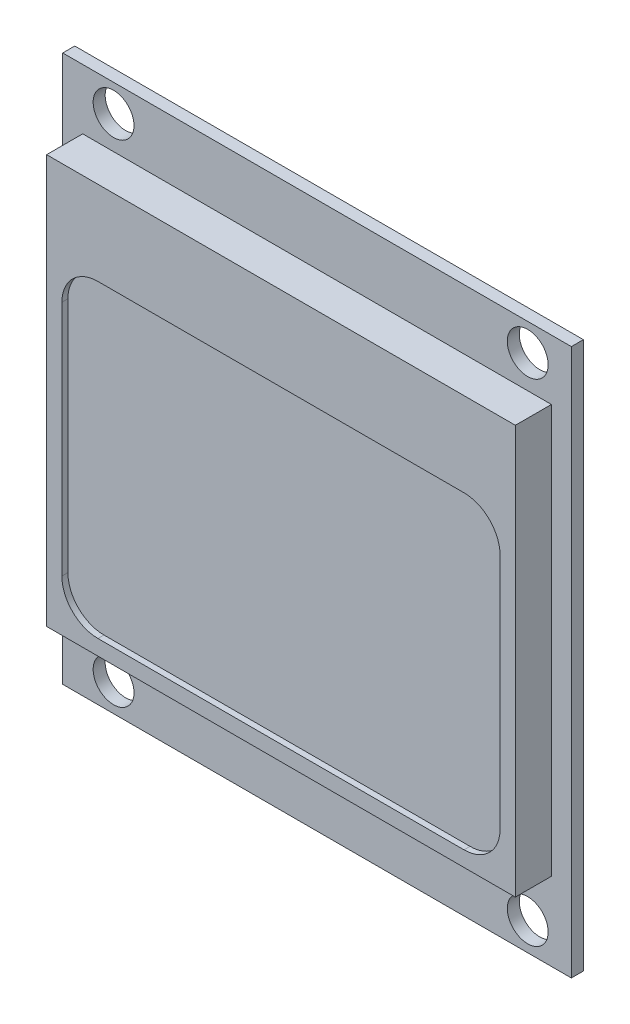
SolidWorks part; units mm, degrees
material "PBT 一般用途"
ref_plane "前视基准面" through (0, 0, 0) normal (0, 0, 1) x (1, 0, 0)
ref_plane "上视基准面" through (0, 0, 0) normal (0, 1, 0) x (1, 0, 0)
ref_plane "右视基准面" through (0, 0, 0) normal (1, 0, 0) x (0, 0, -1)
sketch "草图1" plane through (0, 0, 0) normal (0, 0, 1) x (1, 0, 0)
  line L1 (24.257, 22.0958) -> (44.577, 22.0958)
  line L2 (24.257, 22.0958) -> (24.257, 24.6358)
  line L3 (24.257, 24.6358) -> (44.577, 24.6358)
  line L4 (44.577, 22.0958) -> (44.577, 24.6358)
  point P4 (44.6672, 22.0324)
  point P5 (0, 0)
  point P6 (0, 0)
  point P7 (0, 0)
  point P8 (0, 0)
  dimension "D2" = 20.32
extrude "凸台-拉伸1" add sketch "草图1" along normal blind 11
sketch "草图2" plane through (0, 0, 11) normal (0, 0, 1) x (1, 0, 0)
  line L1 (13.257, 20.0127) -> (55.577, 20.0127)
  line L2 (13.257, 20.0127) -> (13.257, 65.5127)
  line L3 (13.257, 65.5127) -> (55.577, 65.5127)
  line L4 (55.577, 20.0127) -> (55.577, 65.5127)
  line L5 (44.577, 22.0958) -> (44.577, 24.6358) construction
  line L6 (24.257, 24.6358) -> (24.257, 22.0958) construction
  circle A0 centre (17.4869, 22.3607) radius 1.7
  circle A1 centre (51.9469, 22.3607) radius 1.7
  circle A2 centre (17.4869, 63.2357) radius 1.7
  circle A3 centre (51.9469, 63.2357) radius 1.7
  point P4 (0, 0)
  point P22 (0, 0)
  point P23 (0, 0)
  dimension "D4" = 3.4
  dimension "D5" = 3.4
  dimension "D6" = 3.4
  dimension "D7" = 3.4
  dimension "D1" = 11
  dimension "D2" = 11
  dimension "D3" = 45.5
extrude "凸台-拉伸2" add sketch "草图2" along normal blind 1
sketch "草图3" plane through (0, 0, 12) normal (0, 0, 1) x (1, 0, 0)
  line L0 (13.257, 20.0127) -> (55.577, 20.0127) construction
  line L1 (14.917, 60.5127) -> (53.917, 60.5127)
  line L2 (14.917, 60.5127) -> (14.917, 26.5127)
  line L3 (14.917, 26.5127) -> (53.917, 26.5127)
  line L4 (53.917, 60.5127) -> (53.917, 26.5127)
  line L5 (13.257, 65.5127) -> (13.257, 20.0127) construction
  point P4 (53.8931, 26.0271)
  dimension "D1" = 34
  dimension "D2" = 39
  dimension "D3" = 6.5
  dimension "D4" = 1.66
extrude "凸台-拉伸3" add sketch "草图3" along normal blind 3
sketch "草图4" plane through (0, 0, 15) normal (0, 0, 1) x (1, 0, 0)
  line L0 (14.917, 26.5127) -> (53.917, 26.5127) construction
  line L1 (49.647, 27.7827) -> (19.187, 27.7827)
  line L2 (52.647, 30.7827) -> (52.647, 50.5127)
  line L3 (49.647, 53.5127) -> (19.187, 53.5127)
  line L4 (16.187, 30.7827) -> (16.187, 50.5127)
  line L5 (14.917, 60.5127) -> (14.917, 26.5127) construction
  line L6 (53.917, 26.5127) -> (53.917, 60.5127) construction
  line L7 (53.917, 60.5127) -> (14.917, 60.5127) construction
  arc A0 (19.187, 27.7827) -> (16.187, 30.7827) centre (19.187, 30.7827) cw
  arc A1 (19.187, 53.5127) -> (16.187, 50.5127) centre (19.187, 50.5127) ccw
  arc A2 (52.647, 50.5127) -> (49.647, 53.5127) centre (49.647, 50.5127) ccw
  arc A3 (49.647, 27.7827) -> (52.647, 30.7827) centre (49.647, 30.7827) ccw
  point P12 (0, 0)
  dimension "D5" = 3
  dimension "D1" = 1.27
  dimension "D2" = 1.27
  dimension "D3" = 1.27
  dimension "D4" = 7
extrude "切除-拉伸1" cut sketch "草图4" against normal blind 0.5
